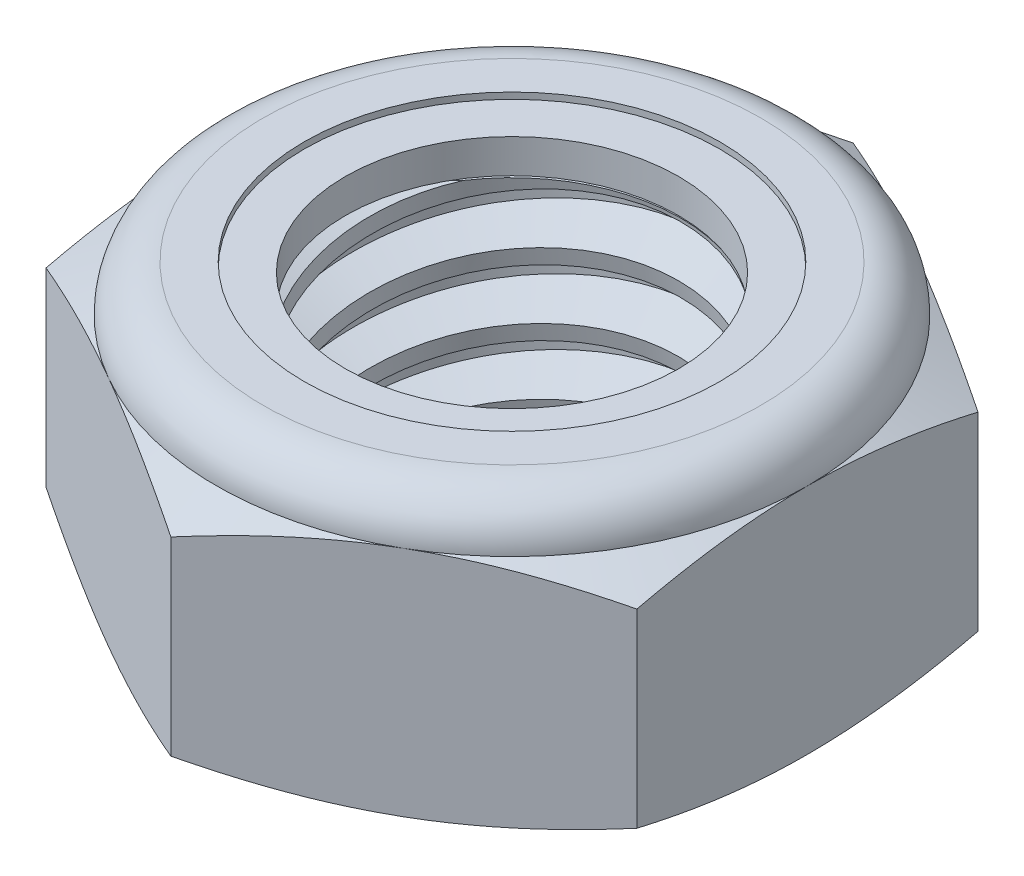
SolidWorks part; units mm, degrees
material "Plain Carbon Steel"
ref_plane "Front" through (0, 0, 0) normal (0, 0, 1) x (1, 0, 0)
ref_plane "Top" through (0, 0, 0) normal (0, 1, 0) x (1, 0, 0)
ref_plane "Right" through (0, 0, 0) normal (1, 0, 0) x (0, 0, -1)
sketch "Sketch1" plane through (0, 0, 0) normal (0, 1, 0) x (1, 0, 0)
  line L1 (0, 8.2489) -> (-7.1438, 4.1244)
  line L2 (-7.1438, 4.1244) -> (-7.1438, -4.1244)
  line L3 (-7.1438, -4.1244) -> (0, -8.2489)
  line L4 (0, -8.2489) -> (7.1437, -4.1244)
  line L5 (7.1437, -4.1244) -> (7.1437, 4.1244)
  line L6 (7.1437, 4.1244) -> (0, 8.2489)
  circle A0 centre (0, 0) radius 7.1438 construction
  dimension "Hex Flats" = 14.2875
extrude "Extrude1" add sketch "Sketch1" along normal blind 6.7469
sketch "Sketch2" plane through (0, 0, 0) normal (1, 0, 0) x (0, 0, -1)
  line L0 (-4.7625, 0) -> (-4.7625, 6.7469) construction
  line L1 (0, 0) -> (4.7625, 0)
  line L2 (0, 0) -> (0, 6.7469)
  line L3 (0, 6.7469) -> (4.7625, 6.7469)
  line L4 (4.7625, 0) -> (4.7625, 6.7469)
  line L5 (-4.1244, 6.7469) -> (4.1244, 6.7469) construction
  line L7 (0, -4.7625) -> (0, 0) construction
  dimension "Thread Dia" = 9.525
revolve "Revolve1" add sketch "Sketch2" angle 360 about L7
sketch "Sketch3" plane through (0, 0, 0) normal (1, 0, 0) x (0, 0, -1)
  line L0 (4.7625, 6.7469) -> (-4.7625, 6.7469) construction
  line L1 (-4.7625, 6.7469) -> (-4.7625, 5.1594) construction
  line L2 (-4.7625, 5.1594) -> (4.7625, 6.7469) construction
  line L3 (4.7625, 6.7469) -> (4.7951, 6.5511) construction
  line L4 (4.7951, 6.5511) -> (5.0235, 5.181)
  line L5 (5.0235, 5.181) -> (4.0944, 5.5291)
  line L6 (4.0944, 5.5291) -> (4.0291, 5.9205)
  line L7 (4.0291, 5.9205) -> (4.7951, 6.5511)
  line L8 (4.0617, 5.7248) -> (4.9093, 5.8661) construction
  line L9 (4.7625, 6.7469) -> (4.7625, 5.8416) construction
  line L10 (4.7625, 5.8416) -> (-4.7625, 4.2541) construction
  line L11 (-4.7625, 4.2541) -> (-4.7625, 5.1594) construction
  line L12 (-0.2832, 6.7469) -> (0.2832, 3.3488) construction
  line L13 (-4.7625, 0) -> (-4.7625, 6.7469) construction
  line L14 (0, 6.7469) -> (4.7625, 6.7469) construction
  line L15 (4.7625, 0) -> (4.7625, 6.7469) construction
  point P13 (0, 5.0478)
  dimension "D1" = 0.1984
  dimension "D2" = 0.3969
  dimension "Thread Pitch" = 1.5875
  dimension "D4" = 60
  dimension "D5" = 1.5875
revolve "Cut-Revolve1" cut sketch "Sketch3" angle 360 about L12
pattern_linear "LPattern1" count 4 spacing 1.5875 along (0, -1, 0) count 2 spacing 1.5875 along (0, 1, 0) of "Cut-Revolve1"
sketch "Sketch4" plane through (0, 0, 0) normal (1, 0, 0) x (0, 0, -1)
  line L0 (0, 6.7469) -> (4.7625, 6.7469)
  line L1 (4.7625, 6.7469) -> (4.0291, 6.4049)
  line L2 (4.0291, 6.4049) -> (4.0291, 0.342)
  line L3 (4.0291, 0.342) -> (4.7625, 0)
  line L4 (4.7625, 0) -> (0, 0)
  line L5 (0, 0) -> (0, 6.7469)
  line L6 (4.7625, 0) -> (4.7625, 6.7469) construction
  line L7 (0, 6.7469) -> (4.7625, 6.7469) construction
  line L8 (0, 0) -> (4.7625, 0) construction
  line L9 (0, 0) -> (0, 6.7469) construction
  line L10 (0, 6.7469) -> (0, 7.5561) construction
  dimension "D1" = 25
revolve "Cut-Revolve2" cut sketch "Sketch4" angle 360 about L10
combine bodies "Combine1" operation type subtract main body 112 bodies to subtract 111
sketch "Sketch5" plane through (0, 0, 0) normal (1, 0, 0) x (0, 0, -1)
  line L0 (0, 0) -> (7.1438, 0)
  line L1 (7.1438, 0) -> (8.2489, 0.5153)
  line L2 (8.2489, 0.5153) -> (8.2489, 5.1071)
  line L3 (8.2489, 5.1071) -> (7.1438, 5.6224)
  line L4 (6.0193, 6.7469) -> (6.0193, 8.0169)
  line L5 (6.0193, 8.0169) -> (9.5189, 8.0169)
  line L6 (9.5189, 8.0169) -> (9.5189, -1.27)
  line L7 (9.5189, -1.27) -> (0, -1.27)
  line L8 (0, -1.27) -> (0, 0)
  line L9 (7.1438, 5.6224) -> (7.1438, 0) construction
  line L10 (0, 0) -> (4.7625, 0) construction
  line L13 (8.2489, 2.8112) -> (9.5189, 2.8112) construction
  line L14 (8.2489, 6.7469) -> (8.2489, 0) construction
  line L15 (0, 0) -> (0, 8.0169) construction
  line L20 (0, 8.0169) -> (6.0193, 8.0169) construction
  line L22 (0, 6.7469) -> (4.7625, 6.7469) construction
  arc A0 (7.1438, 5.6224) -> (6.0193, 6.7469) centre (6.0193, 5.6224) ccw
  dimension "D1" = 25
  dimension "D2" = 1.27
  dimension "D3" = 6.7469
  dimension "D4" = 1.1245
revolve "Cut-Revolve3" cut sketch "Sketch5" angle 360 about L15
sketch "Sketch6" plane through (0, 0, 0) normal (1, 0, 0) x (0, 0, -1)
  line L0 (0, 5.6224) -> (6.9914, 5.6224)
  line L1 (6.0193, 6.5945) -> (5.0242, 6.5945)
  line L2 (0, 8.0169) -> (0, 5.6224)
  line L3 (5.0242, 8.0169) -> (0, 8.0169)
  line L4 (0, 8.0169) -> (6.0193, 8.0169) construction
  line L5 (0, 0) -> (0, 8.0169) construction
  line L6 (0, 8.0169) -> (0, 44.323) construction
  line L7 (5.0242, 6.5945) -> (5.0242, 8.0169)
  line L8 (6.0193, 6.7469) -> (6.0193, 6.5945) construction
  line L9 (5.0242, 6.5945) -> (4.0291, 6.5945) construction
  line L10 (4.0291, 6.5945) -> (4.0291, 6.4049) construction
  arc A0 (6.9914, 5.6224) -> (6.0193, 6.5945) centre (6.0193, 5.6224) ccw
  arc A1 (7.1438, 5.6224) -> (6.0193, 6.7469) centre (6.0193, 5.6224) ccw construction
  dimension "D1" = 0.1524
revolve "Cut-Revolve4" cut sketch "Sketch6" angle 360 about L6
sketch "Sketch7" plane through (0, 0, 0) normal (1, 0, 0) x (0, 0, -1)
  line L0 (4.0291, 5.6986) -> (6.9119, 5.6986)
  line L1 (6.0193, 6.5183) -> (4.0291, 6.5183)
  line L2 (4.0291, 6.5183) -> (4.0291, 5.6986)
  line L3 (4.0291, 5.6986) -> (0, 5.6986) construction
  line L4 (0, 5.6986) -> (0, 6.5183) construction
  line L5 (0, 6.5183) -> (4.0291, 6.5183) construction
  line L6 (4.0291, 5.6986) -> (4.0291, 5.6224) construction
  line L7 (0, 5.6224) -> (6.9914, 5.6224) construction
  line L8 (6.0193, 6.5183) -> (6.0193, 6.5945) construction
  arc A0 (6.9119, 5.6986) -> (6.0193, 6.5183) centre (6.0193, 5.6224) ccw
  arc A2 (6.9914, 5.6224) -> (6.0193, 6.5945) centre (6.0193, 5.6224) ccw construction
  dimension "D1" = 0.0762
revolve "Revolve2" add sketch "Sketch7" angle 360 about L4
equation "\"D1@Sketch3\"=\"Thread Pitch@Sketch3\"/8"
equation "\"D2@Sketch3\"=\"Thread Pitch@Sketch3\"/4"
equation "\"D5@Sketch3\"=\"Thread Pitch@Sketch3\""
equation "\"D4@LPattern1\"=\"Thread Pitch@Sketch3\""
equation "\"D3@LPattern1\"=\"Thread Pitch@Sketch3\""
equation "\"D1@LPattern1\"=\"Height@Extrude1\"/\"Thread Pitch@Sketch3\""
equation "\"D4@Sketch5\"=\"Height@Extrude1\"/6"
